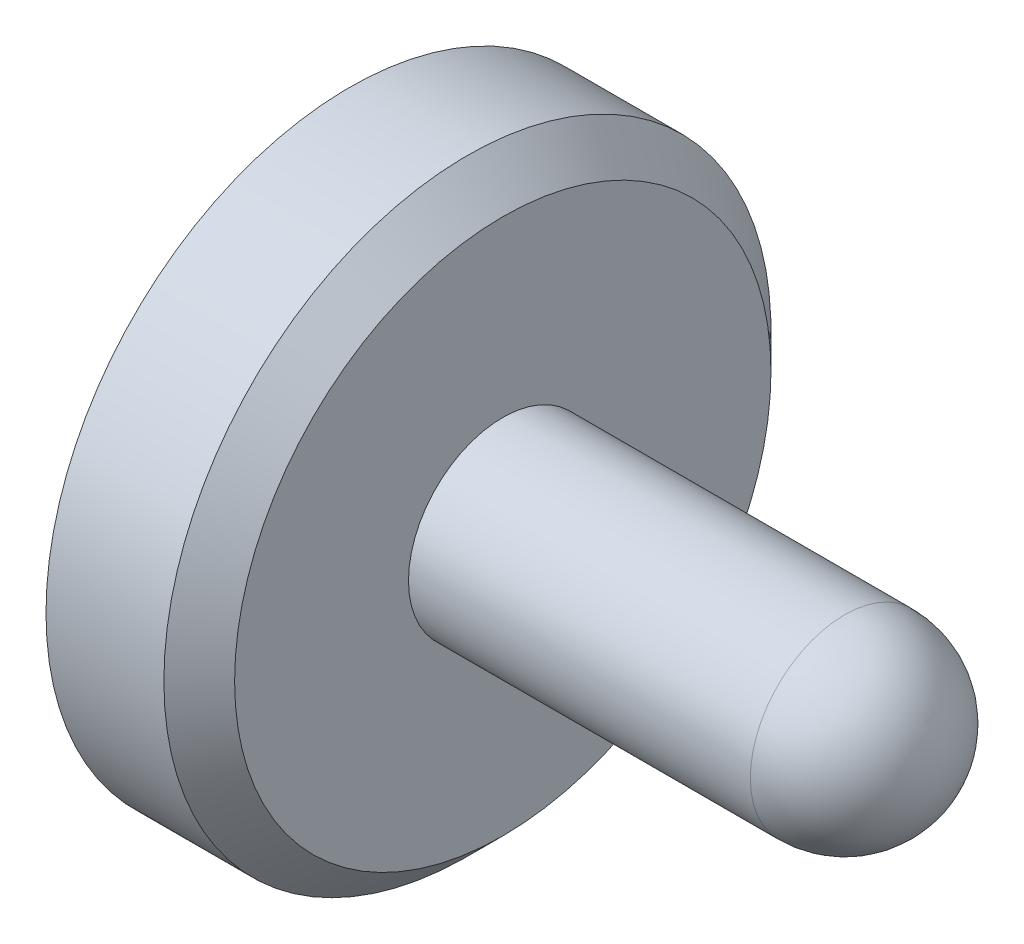
SolidWorks part; units mm, degrees
material "Brass Alloy 385"
ref_plane "Front Plane" through (0, 0, 0) normal (0, 0, 1) x (1, 0, 0)
ref_plane "Top Plane" through (0, 0, 0) normal (0, 1, 0) x (1, 0, 0)
ref_plane "Right Plane" through (0, 0, 0) normal (1, 0, 0) x (0, 0, -1)
sketch "Sketch1" plane through (0, 0, 0) normal (0, 0, 1) x (1, 0, 0)
  line L0 (0, 0) -> (0, 0.6541)
  line L1 (0, 0.6541) -> (0.254, 0.6541)
  line L2 (0.3302, 0.5779) -> (0.3302, 0.2032)
  line L3 (0.3302, 0.2032) -> (1.0668, 0.2032)
  line L4 (0, 0) -> (1.27, 0)
  line L5 (0, 0) -> (1.27, 0) construction
  line L6 (0.254, 0.6541) -> (0.3302, 0.5779)
  arc A0 (1.27, 0) -> (1.0668, 0.2032) centre (1.0668, 0) ccw
revolve "RevolutionAngle1" add sketch "Sketch1" angle 360 about L5
